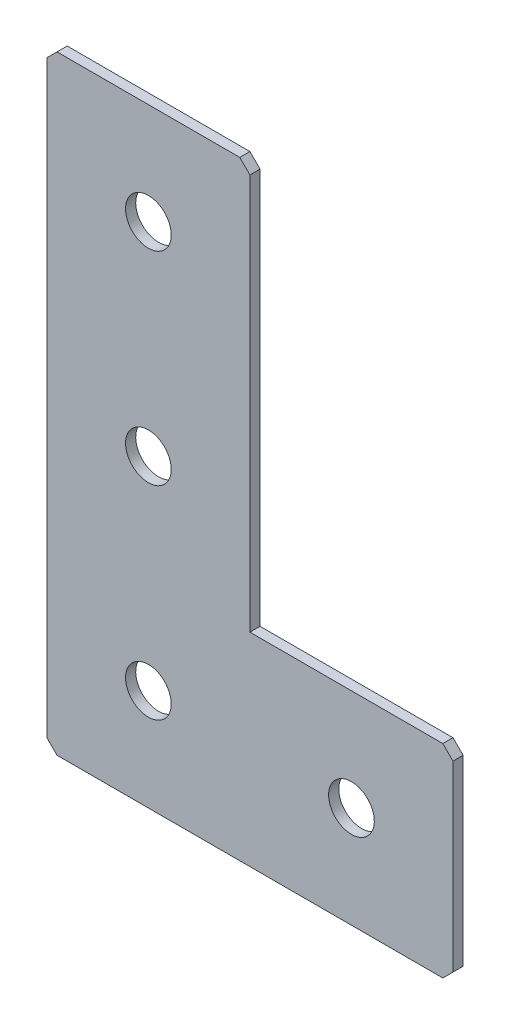
SolidWorks part; units mm, degrees
material "Простая углеродистая сталь"
ref_plane "Спереди(Плоскость XY)" through (0, 0, 0) normal (0, 0, 1) x (1, 0, 0)
ref_plane "Сверху(Плоскость XZ)" through (0, 0, 0) normal (0, 1, 0) x (1, 0, 0)
ref_plane "Справа(Плоскость ZY)" through (0, 0, 0) normal (1, 0, 0) x (0, 0, -1)
sketch "Эскиз1" plane through (0, 0, 0) normal (0, 0, -1) x (1, 0, 0)
  line L0 (0, 0) -> (0, 120)
  line L1 (0, 120) -> (80, 120)
  line L2 (80, 120) -> (80, 80)
  line L3 (80, 80) -> (40, 80)
  line L4 (40, 80) -> (40, 0)
  line L5 (40, 0) -> (0, 0)
  dimension "D1" = 120
  dimension "D2" = 40
  dimension "D3" = 40
  dimension "D4" = 40
extrude "Бобышка-Вытянуть1" add sketch "Эскиз1" along normal blind 2
hole_wizard "Отверстие с зазором M81" positions "Эскиз2" profile "Эскиз3" hole size "M8" standard "DIN" end condition through all
sketch "Эскиз2" plane through (0, 0, -2) normal (0, 0, -1) x (1, 0, 0)
  line L1 (0, 0) -> (40, 0) construction
  line L6 (0, 120) -> (0, 0) construction
  point P0 (60, 100)
  point P2 (20, 100)
  point P4 (20, 60)
  point P6 (20, 20)
  dimension "D1" = 40
  dimension "D2" = 40
  dimension "D3" = 40
  dimension "D4" = 20
  dimension "D5" = 20
sketch "Эскиз3" plane through (60, -100, -2) normal (1, 0, 0) x (0, 1, 0)
  line L0 (0, 0) -> (0, 2)
  line L1 (0, 2) -> (4.5, 2)
  line L2 (4.5, 2) -> (4.5, 0)
  line L5 (4.5, 0) -> (0, 0)
  line L11 (0, -6.35) -> (0, 107.95) construction
  dimension "Диаметр сквозного отверстия" = 9
  dimension "Глубина сквозного отверстия" = 2
chamfer "Фаска1" distance 2 angle 45 5 edges at (0, 0, -1) (40, 0, -1) (80, -80, -1) (80, -120, -1) (0, -120, -1)
